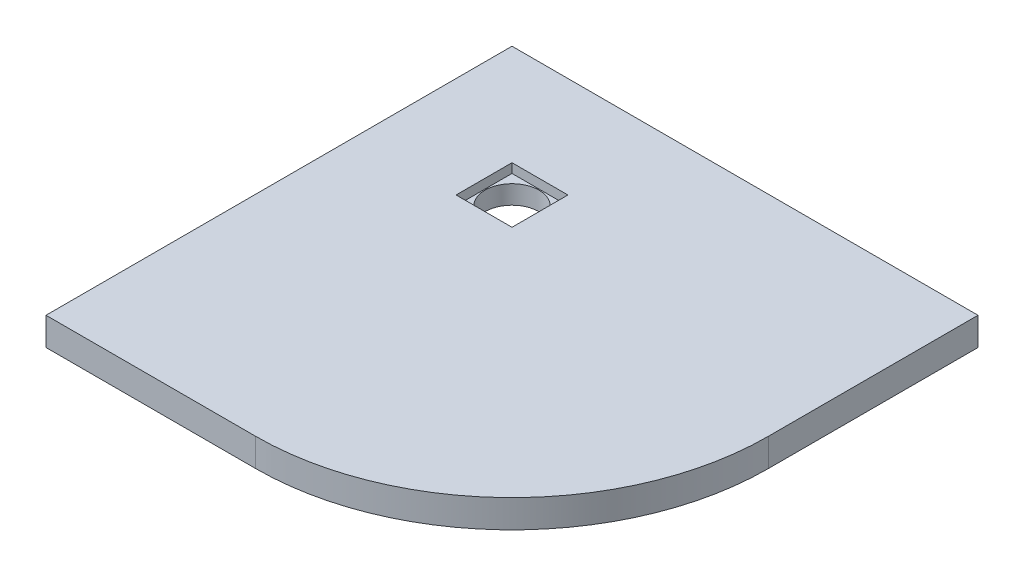
SolidWorks part; units mm, degrees
ref_plane "Ebene vorne" through (0, 0, 0) normal (0, 0, 1) x (1, 0, 0)
ref_plane "Ebene oben" through (0, 0, 0) normal (0, 1, 0) x (1, 0, 0)
ref_plane "Ebene rechts" through (0, 0, 0) normal (1, 0, 0) x (0, 0, -1)
sketch "Skizze1" plane through (0, 0, 0) normal (0, 0, 1) x (1, 0, 0)
  line L1 (0, 0) -> (1000, 0)
  line L2 (0, 0) -> (0, 60)
  line L3 (0, 60) -> (1000, 60)
  line L4 (1000, 0) -> (1000, 60)
  dimension "D1" = 1000
  dimension "D2" = 60
extrude "Aufsatz-Linear austragen1" add sketch "Skizze1" along normal blind 1000
sketch "Skizze2" plane through (0, 60, 0) normal (0, 1, 0) x (1, 0, 0)
  line L0 (1000, -1000) -> (1000, -450)
  line L1 (1000, -1000) -> (1000, 0) construction
  line L3 (1000, -1000) -> (0, -1000) construction
  line L4 (450, -1000) -> (1000, -1000)
  arc A0 (450, -1000) -> (1000, -450) centre (450, -450) ccw
  dimension "D3" = 550
  dimension "D1" = 550
  dimension "D2" = 550
extrude "Schnitt-Linear austragen1" cut sketch "Skizze2" against normal blind 1000
sketch "Skizze3" plane through (0, 60, 0) normal (0, 1, 0) x (1, 0, 0)
  line L0 (1000, 0) -> (0, 0) construction
  line L1 (0, -1000) -> (0, 0) construction
  circle A0 centre (276.5, -276.5) radius 58
  dimension "D3" = 116
  dimension "D1" = 276.5
  dimension "D2" = 276.5
extrude "Schnitt-Linear austragen2" cut sketch "Skizze3" against normal through all
sketch "Skizze4" plane through (0, 60, 0) normal (0, 1, 0) x (1, 0, 0)
  line L1 (216.5, -336.5) -> (336.5, -336.5)
  line L2 (216.5, -336.5) -> (216.5, -216.5)
  line L3 (216.5, -216.5) -> (336.5, -216.5)
  line L4 (336.5, -336.5) -> (336.5, -216.5)
  circle A0 centre (276.5, -276.5) radius 58 construction
  dimension "D3" = 60
  dimension "D4" = 60
  dimension "D1" = 120
  dimension "D2" = 120
extrude "Schnitt-Linear austragen3" cut sketch "Skizze4" against normal blind 20
sketch "Skizze13" plane through (0, 60, 0) normal (0, 1, 0) x (1, 0, 0)
  line L0 (450, -1000) -> (0, -1000)
  line L1 (450, -1000) -> (0, -1000) construction
  line L2 (0, -1000) -> (216.5, -336.5)
  line L3 (216.5, -336.5) -> (336.5, -216.5)
  line L4 (336.5, -216.5) -> (1000, 0)
  line L5 (1000, -450) -> (1000, 0) construction
  line L6 (1000, 0) -> (1000, -450)
  arc A0 (1000, -450) -> (450, -1000) centre (450, -450) cw
  arc A1 (450, -1000) -> (1000, -450) centre (450, -450) ccw construction
sketch "Skizze14" plane through (0, 40, 0) normal (0, 1, 0) x (1, 0, 0)
  line L0 (0, -33) -> (0, 33) construction
  circle A0 centre (276.5, -276.5) radius 58
